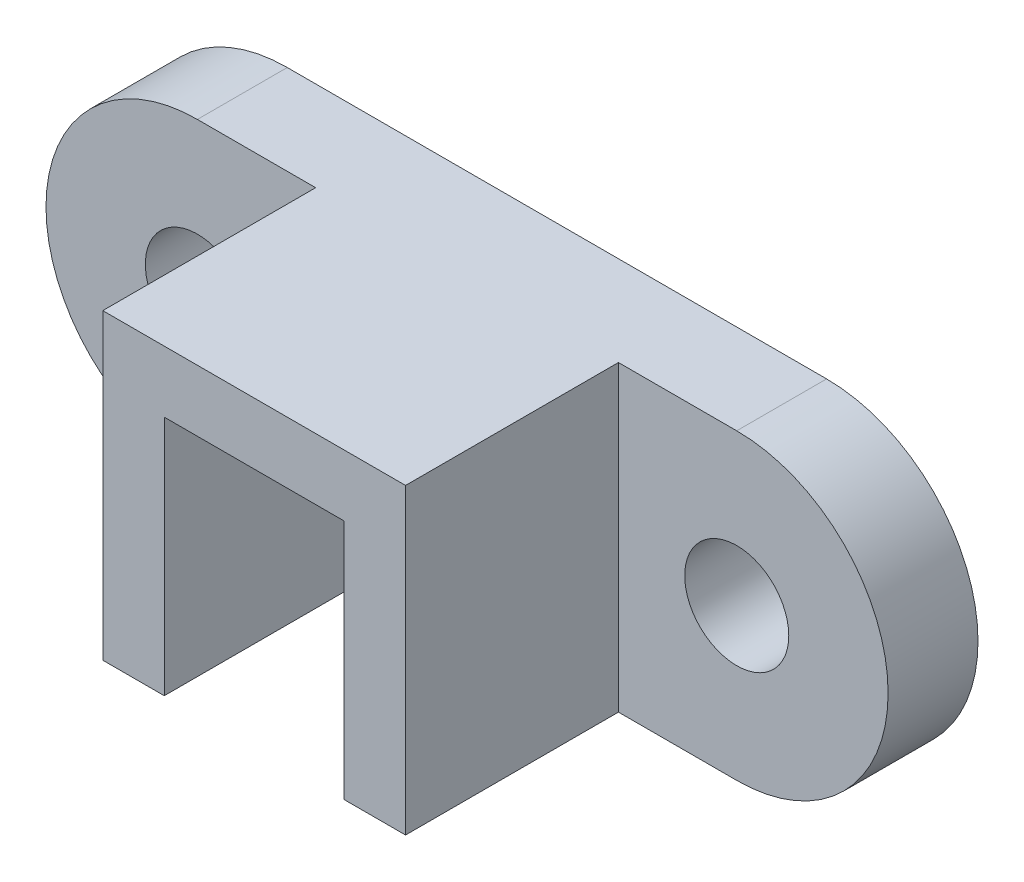
SolidWorks part; units mm, degrees
ref_plane "Front Plane" through (0, 0, 0) normal (0, 0, 1) x (1, 0, 0)
ref_plane "Top Plane" through (0, 0, 0) normal (0, 1, 0) x (1, 0, 0)
ref_plane "Right Plane" through (0, 0, 0) normal (1, 0, 0) x (0, 0, -1)
sketch "Sketch1" plane through (0, 0, 0) normal (0, 0, 1) x (1, 0, 0)
  line L0 (-57, 0) -> (57, 0) construction
  line L1 (-57, 32) -> (57, 32)
  line L2 (-57, -32) -> (57, -32)
  arc A0 (-57, 32) -> (-57, -32) centre (-57, 0) ccw
  arc A1 (57, -32) -> (57, 32) centre (57, 0) ccw
  point P3 (0, 0)
  dimension "D2" = 32
  dimension "D1" = 114
extrude "Boss-Extrude1" add sketch "Sketch1" along normal blind 19
sketch "Sketch2" plane through (0, 0, 19) normal (0, 0, 1) x (1, 0, 0)
  line L0 (57, 32) -> (57, -32) construction
  line L1 (-89, 0) -> (89, 0) construction
  line L2 (-57, 32) -> (-57, -32) construction
  circle A0 centre (-57, 0) radius 11
  arc A1 (-57, 32) -> (-57, -32) centre (-57, 0) ccw construction
  arc A2 (57, -32) -> (57, 32) centre (57, 0) ccw construction
  circle A3 centre (57, 0) radius 11
  dimension "D1" = 22
  dimension "D2" = 22
extrude "Cut-Extrude1" cut sketch "Sketch2" against normal through all
sketch "Sketch4" plane through (0, 0, 0) normal (0, 0, 1) x (1, 0, 0)
  line L0 (-89, 0) -> (89, 0) construction
  line L1 (0, 32) -> (0, -32) construction
  line L2 (57, 32) -> (-57, 32) construction
  line L3 (-57, -32) -> (57, -32) construction
  arc A0 (-57, 32) -> (-57, -32) centre (-57, 0) ccw construction
  arc A1 (57, -32) -> (57, 32) centre (57, 0) ccw construction
sketch "Sketch5" plane through (0, 0, 19) normal (0, 0, 1) x (1, 0, 0)
  line L0 (-32, 32) -> (-32, -32)
  line L1 (57, 32) -> (-57, 32) construction
  line L2 (-57, -32) -> (57, -32) construction
  line L3 (-32, -32) -> (0, -32)
  line L4 (0, -32) -> (0, 32)
  line L5 (0, 32) -> (-32, 32)
  line L6 (-32, 32) -> (0, -32) construction
  line L7 (-32, -32) -> (0, 32) construction
  line L8 (0, 32) -> (0, -32) construction
  point P9 (32, -32)
  dimension "D1" = 32
extrude "Boss-Extrude4" add sketch "Sketch5" along normal blind 45
sketch "Sketch8" plane through (0, 0, 0) normal (1, 0, 0) x (0, 0, -1)
  line L0 (-13, -32) -> (-64, 19)
  line L1 (-64, -32) -> (-64, 32) construction
  line L6 (-13, -32) -> (-64, -32)
  line L7 (-64, -32) -> (-64, 19)
  dimension "D1" = 13
  dimension "D2" = 13
extrude "Cut-Extrude3" cut sketch "Sketch8" against normal blind 19
ref_plane "Plane2" through (0, 0, 0) normal (1, 0, 0) x (0, 0, -1)
mirror "Mirror2" about plane through (0, 0, 0) normal (1, 0, 0) of "Cut-Extrude3", "Boss-Extrude4"
